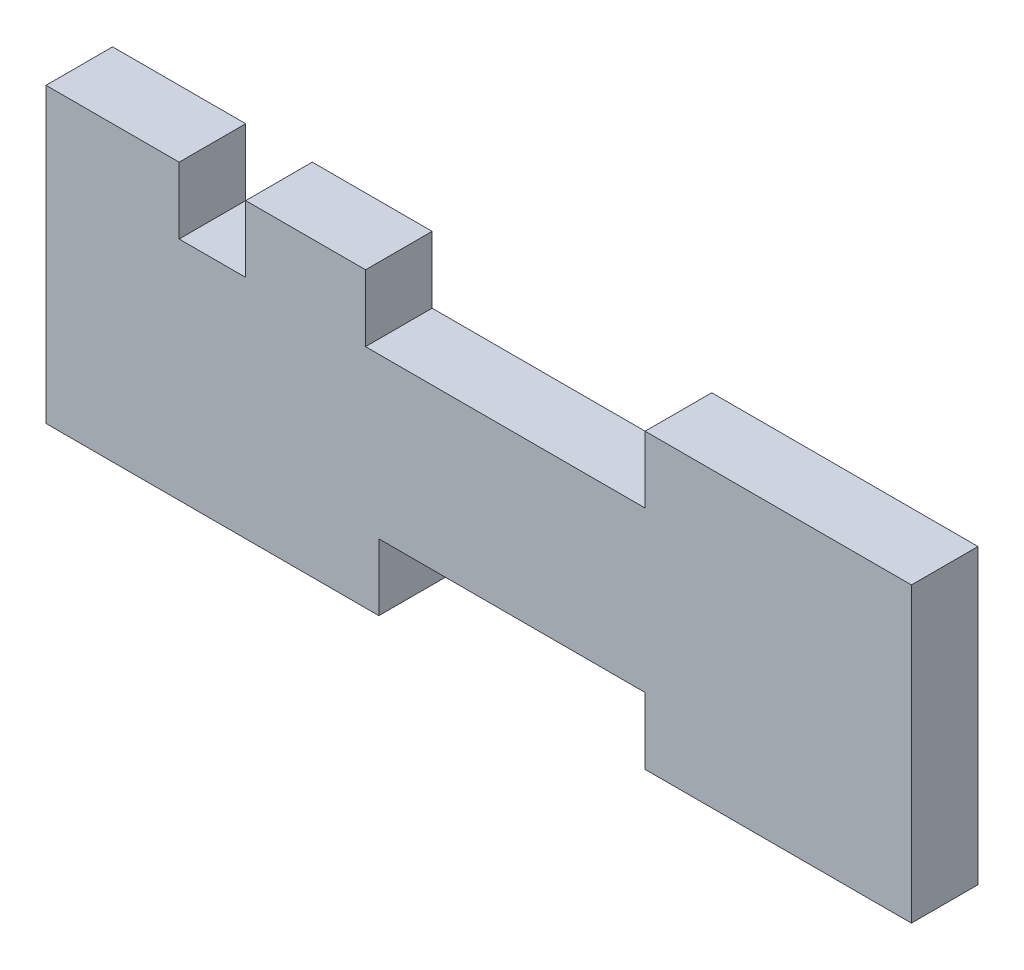
SolidWorks part; units mm, degrees
ref_plane "Front Plane" through (0, 0, 0) normal (0, 0, 1) x (1, 0, 0)
ref_plane "Top Plane" through (0, 0, 0) normal (0, 1, 0) x (1, 0, 0)
ref_plane "Right Plane" through (0, 0, 0) normal (1, 0, 0) x (0, 0, -1)
sketch "Sketch1" plane through (0, 0, 0) normal (0, 0, 1) x (1, 0, 0)
  line L1 (0, 0) -> (-65, 0)
  line L2 (0, 0) -> (0, 12)
  line L3 (0, 12) -> (-65, 12)
  line L4 (-65, 0) -> (-65, 12)
  line L5 (-65, 12) -> (-40, 12)
  line L6 (-65, 12) -> (-65, 17)
  line L7 (-65, 17) -> (-40, 17)
  line L8 (-40, 12) -> (-40, 17)
  line L9 (-55, 17) -> (-50, 17)
  line L10 (-55, 17) -> (-55, 12)
  line L11 (-55, 12) -> (-50, 12)
  line L12 (-50, 17) -> (-50, 12)
  line L13 (0, 12) -> (-20, 12)
  line L14 (0, 12) -> (0, 17)
  line L15 (0, 17) -> (-20, 17)
  line L16 (-20, 12) -> (-20, 17)
  line L17 (0, 0) -> (-20, 0)
  line L18 (0, 0) -> (0, -5)
  line L19 (0, -5) -> (-20, -5)
  line L20 (-20, 0) -> (-20, -5)
  line L21 (-65, 0) -> (-40, 0)
  line L22 (-65, 0) -> (-65, -5)
  line L23 (-65, -5) -> (-40, -5)
  line L24 (-40, 0) -> (-40, -5)
  dimension "D1" = 65
  dimension "D2" = 12
  dimension "D3" = 25
  dimension "D4" = 5
  dimension "D5" = 5
  dimension "D6" = 10
  dimension "D7" = 20
  dimension "D8" = 20
  dimension "D9" = 5
  dimension "D10" = 25
  dimension "D11" = 5
  dimension "D12" = 5
extrude "Boss-Extrude1" add sketch "Sketch1" along normal blind 5 contours L4 L1 L2 L3 L5 | L10 L7 L6 L5 | L7 L12 L3 L8 | L24 L1 L22 L23 | L1 L20 L19 L18 | L16 L3 L14 L15
sketch "Sketch2" plane through (-40, 0, 0) normal (1, 0, 0) x (0, 0, -1)
  line L4 (0, 12) -> (0, 17)
  line L5 (0, 17) -> (-5, 17)
  line L6 (-5, 17) -> (-5, 12)
  line L7 (-5, 12) -> (0, 12)
  line L8 (0, 12) -> (0, 17)
  line L9 (0, 17) -> (-5, 17)
  line L10 (-5, 17) -> (-5, 12)
  line L11 (-5, 12) -> (0, 12)
  dimension "D1" = 0
extrude "Cut-Extrude1" cut sketch "Sketch2" against normal blind 1
